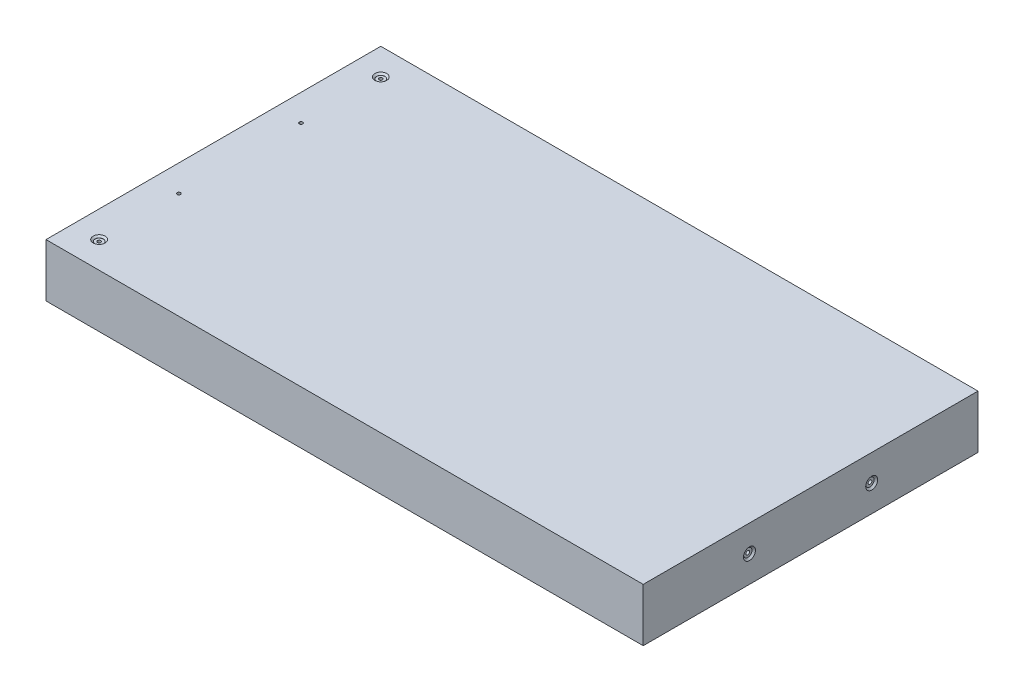
SolidWorks part; units mm, degrees
material "Balsa"
ref_plane "Front Plane" through (0, 0, 0) normal (0, 0, 1) x (1, 0, 0)
ref_plane "Top Plane" through (0, 0, 0) normal (0, 1, 0) x (1, 0, 0)
ref_plane "Right Plane" through (0, 0, 0) normal (1, 0, 0) x (0, 0, -1)
sketch "Sketch1" plane through (0, 0, 0) normal (0, 1, 0) x (1, 0, 0)
  line L1 (-142.7, 80) -> (142.7, 80)
  line L2 (-142.7, 80) -> (-142.7, -80)
  line L3 (-142.7, -80) -> (142.7, -80)
  line L4 (142.7, 80) -> (142.7, -80)
  line L5 (-142.7, 80) -> (142.7, -80) construction
  line L6 (-142.7, -80) -> (142.7, 80) construction
  point P0 (0, 0)
  dimension "D1" = 285.4
  dimension "D2" = 160
extrude "Boss-Extrude1" add sketch "Sketch1" along normal blind 25.4
hole_wizard "CBORE for #0 Binding Head Machine Screw3" positions "Sketch2" profile "Sketch3" counterbore size "#0" standard "ANSI Inch"
sketch "Sketch2" plane through (142.7, 0, 0) normal (1, 0, 0) x (0, 0, -1)
  line L0 (-80, 25.4) -> (-80, 0) construction
  point P0 (-29.2, 12.7)
  point P2 (29.2, 12.7)
  point P11 (-80, 12.7)
  dimension "D1" = 58.4
  dimension "D2" = 50.8
sketch "Sketch3" plane through (142.7, 12.7, 29.2) normal (0, 1, 0) x (0, 0, -1)
  line L0 (0, 0) -> (0, 30.5342)
  line L1 (0, 30.5342) -> (0.889, 30)
  line L2 (0.889, 30) -> (0.889, 0.8128)
  line L3 (0.889, 0.8128) -> (1.985, 0.8128)
  line L5 (1.985, 0.8128) -> (1.985, 0.8725)
  line L6 (1.985, 0.8725) -> (2.8575, 0)
  line L7 (2.8575, 0) -> (0, 0)
  line L8 (-1.985, 0.8725) -> (-2.8575, 0) construction
  line L10 (0, 30.5342) -> (-0.889, 30) construction
  line L11 (0, -6.35) -> (0, 107.95) construction
  dimension "Hole Dia." = 1.778
  dimension "Hole Depth" = 30
  dimension "C'Bore Dia." = 3.97
  dimension "C'Bore Depth" = 0.8128
  dimension "Near C'Sink Dia." = 5.715
  dimension "Near C'Sink Angle" = 90
  dimension "Drill Angle" = 118
hole_wizard "CBORE for #0 Binding Head Machine Screw1" positions "Sketch6" profile "Sketch7" counterbore size "#0" standard "ANSI Inch" end condition through all
sketch "Sketch6" plane through (0, 25.4, 0) normal (0, 1, 0) x (1, 0, 0)
  line L0 (-142.7, -80) -> (142.7, -80) construction
  line L1 (-142.7, 80) -> (-142.7, -80) construction
  line L2 (142.7, 80) -> (-142.7, 80) construction
  point P0 (-130, -67.3)
  point P2 (-130, 67.3)
  dimension "D1" = 12.7
  dimension "D2" = 12.7
  dimension "D3" = 12.7
sketch "Sketch7" plane through (-130, 25.4, 67.3) normal (1, 0, 0) x (0, 0, 1)
  line L0 (0, 0) -> (0, 25.4)
  line L1 (0, 25.4) -> (0.8064, 25.4)
  line L3 (0.8064, 25.4) -> (0.8065, 0.8128)
  line L4 (1.985, 0.8128) -> (0.8065, 0.8128)
  line L5 (1.985, 0.8128) -> (1.985, 0.7321)
  line L6 (1.985, 0.7321) -> (2.8575, 0)
  line L7 (2.8575, 0) -> (0, 0)
  line L8 (-1.985, 0.7321) -> (-2.8575, 0) construction
  line L11 (0, -6.35) -> (0, 107.95) construction
  dimension "Thru Hole Dia." = 1.6129
  dimension "Thru Hole Depth" = 25.4
  dimension "C'Bore Dia." = 3.97
  dimension "C'Bore Depth" = 0.8128
  dimension "Near C'Sink Dia." = 5.715
  dimension "Near C'Sink Angle" = 100
hole_wizard "CBORE for #0 Binding Head Machine Screw2" positions "Sketch8" profile "Sketch9" counterbore size "#0" standard "ANSI Inch" end condition through all
sketch "Sketch8" plane through (0, 0, 0) normal (0, -1, 0) x (-1, 0, 0)
  line L0 (-142.7, 80) -> (142.7, 80) construction
  line L1 (142.7, -80) -> (-142.7, -80) construction
  line L2 (142.7, 80) -> (142.7, -80) construction
  point P0 (130, 29.2)
  point P2 (130, -29.2)
  dimension "D1" = 50.8
  dimension "D2" = 50.8
  dimension "D3" = 12.7
  dimension "D4" = 12.7
sketch "Sketch9" plane through (-130, 0, -29.2) normal (1, 0, 0) x (0, 0, -1)
  line L0 (0, 0) -> (0, 25.4)
  line L1 (0, 25.4) -> (0.8064, 25.4)
  line L3 (0.8064, 25.4) -> (0.8065, 0.8128)
  line L4 (1.985, 0.8128) -> (0.8065, 0.8128)
  line L5 (1.985, 0.8128) -> (1.985, 0.7321)
  line L6 (1.985, 0.7321) -> (2.8575, 0)
  line L7 (2.8575, 0) -> (0, 0)
  line L8 (-1.985, 0.7321) -> (-2.8575, 0) construction
  line L11 (0, -6.35) -> (0, 107.95) construction
  dimension "Thru Hole Dia." = 1.6129
  dimension "Thru Hole Depth" = 25.4
  dimension "C'Bore Dia." = 3.97
  dimension "C'Bore Depth" = 0.8128
  dimension "Near C'Sink Dia." = 5.715
  dimension "Near C'Sink Angle" = 100
